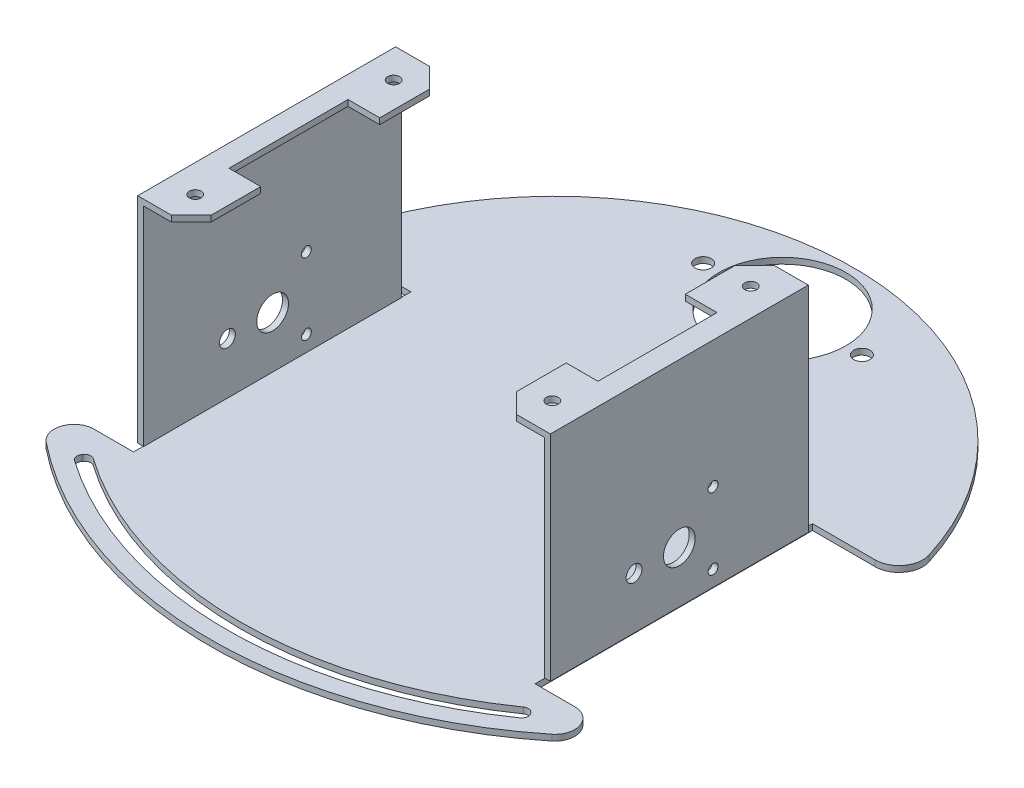
SolidWorks part; units mm, degrees
material "3.3535 (EN-AW 5754)"
ref_plane "Спереди" through (0, 0, 0) normal (0, 0, 1) x (1, 0, 0)
ref_plane "Сверху" through (0, 0, 0) normal (0, 1, 0) x (1, 0, 0)
ref_plane "Справа" through (0, 0, 0) normal (1, 0, 0) x (0, 0, -1)
sketch "Эскиз1" plane through (0, 0, 0) normal (0, 1, 0) x (1, 0, 0)
  line L0 (-50.6, 0) -> (-50.6, 34.95)
  line L1 (-50.6, 0) -> (-50.6, -34.95)
  line L2 (-50.6, -34.95) -> (-56.7978, -34.95)
  line L3 (50.6, 0) -> (50.6, 34.95)
  line L4 (50.6, 0) -> (50.6, -34.95)
  line L5 (50.6, -34.95) -> (60.5883, -34.95)
  line L14 (50.6, 34.95) -> (66.053, 34.95)
  line L15 (50.6, 34.95) -> (66.3145, 34.95)
  line L16 (50.6, 34.95) -> (66.053, 34.95)
  line L17 (50.6, 34.95) -> (66.4232, 34.95)
  line L18 (-50.6, 34.95) -> (-66.4232, 34.95)
  line L19 (-50.6, -34.95) -> (-60.5883, -34.95)
  line L20 (0, 0) -> (0, 1) construction
  line L21 (0, 0) -> (1, 0) construction
  arc A0 (72.1576, 42.7155) -> (-72.1576, 42.7155) centre (0, 20.5) ccw
  circle A1 centre (0, 78) radius 16
  arc A2 (-72.1576, 42.7155) -> (-66.4232, 34.95) centre (-66.4232, 40.95) ccw
  arc A3 (66.4232, 34.95) -> (72.1576, 42.7155) centre (66.4232, 40.95) ccw
  arc A4 (-60.5883, -34.95) -> (-63.7114, -43.8546) centre (-60.5883, -39.95) ccw
  arc A5 (63.7114, -43.8546) -> (60.5883, -34.95) centre (60.5883, -39.95) ccw
  arc A6 (-63.7114, -43.8546) -> (63.7114, -43.8546) centre (0, 35.8) ccw
extrude "Бобышка-Вытянуть1" add sketch "Эскиз1" along normal blind 1.5
sketch "Эскиз3" plane through (0, 0, 0) normal (0, 1, 0) x (1, 0, 0)
  line L0 (-52, 0) -> (-52, 32.5)
  line L1 (-52, 32.5) -> (-50.5, 32.5)
  line L2 (-50.5, 32.5) -> (-50.5, -32.5)
  line L3 (-50.5, -32.5) -> (-52, -32.5)
  line L4 (-52, -32.5) -> (-52, 0)
  line L5 (0, 0) -> (0, -12.5711) construction
  line L6 (0, 0) -> (8.0553, 0) construction
  line L7 (52, -32.5) -> (52, 0)
  line L8 (50.5, -32.5) -> (52, -32.5)
  line L9 (50.5, 32.5) -> (50.5, -32.5)
  line L10 (52, 32.5) -> (50.5, 32.5)
  line L11 (52, 0) -> (52, 32.5)
  dimension "D1" = 1.5
  dimension "D2" = 32.5
  dimension "D3" = 65
  dimension "D4" = 1.5
extrude "Бобышка-Вытянуть2" add sketch "Эскиз3" along normal blind 53.5 from offset 1.5
sketch "Эскиз5" plane through (0, 0, 0) normal (1, 0, 0) x (0, 0, -1)
  line L0 (0, 0) -> (0, 14.5) construction
  circle A0 centre (0, 14.5) radius 4
  dimension "D1" = 14.5
extrude "Вырез-Вытянуть1" cut sketch "Эскиз5" against normal through all and the other way blind 54
sketch "Эскиз6" plane through (0, 0, 0) normal (0, 1, 0) x (1, 0, 0)
  line L0 (0, 0) -> (0, 32.0086) construction
  line L1 (-3.4237, 0) -> (71.1887, 0) construction
  line L3 (-52, 32.5) -> (-52, -32.5) construction
  line L4 (-52, 0) -> (-52, 32.5)
  line L5 (-52, 32.5) -> (-38.5, 32.5)
  line L6 (-38.5, 32.5) -> (-38.5, 0)
  line L7 (-52, 0) -> (-52, -32.5)
  line L8 (-52, -32.5) -> (-38.5, -32.5)
  line L9 (-38.5, -32.5) -> (-38.5, 0)
  line L10 (-38.5, 15) -> (-46.5, 15)
  line L11 (-46.5, 15) -> (-46.5, 0)
  line L12 (-38.5, -15) -> (-46.5, -15)
  line L13 (-46.5, -15) -> (-46.5, 0)
  line L14 (46.5, -15) -> (46.5, 0)
  line L15 (38.5, -15) -> (46.5, -15)
  line L16 (46.5, 15) -> (46.5, 0)
  line L17 (38.5, 15) -> (46.5, 15)
  line L18 (38.5, -32.5) -> (38.5, 0)
  line L19 (52, -32.5) -> (38.5, -32.5)
  line L20 (52, 0) -> (52, -32.5)
  line L21 (38.5, 32.5) -> (38.5, 0)
  line L22 (52, 32.5) -> (38.5, 32.5)
  line L23 (52, 0) -> (52, 32.5)
  dimension "D2" = 30
  dimension "D1" = 13.5
  dimension "D3" = 15
  dimension "D4" = 8
  dimension "D5" = 8
extrude "Бобышка-Вытянуть3" add sketch "Эскиз6" against normal blind 1.5 from offset 55.5 contours L12 L13 L11 L10 L6 L5 L4 L7 L8 L9 | L20 L23 L22 L21 L17 L16 L14 L15 L18 L19
sketch "Эскиз9" plane through (0, 0, 0) normal (0, 1, 0) x (1, 0, 0)
  line L0 (45, 0) -> (-45, 0) construction
  line L1 (-45, -25) -> (-45, 25) construction
  line L2 (0, 0) -> (0, 4.277) construction
  line L3 (45, -25) -> (45, 25) construction
  circle A0 centre (-45, 25) radius 1.5
  circle A1 centre (-45, -25) radius 1.5
  circle A2 centre (45, -25) radius 1.5
  circle A3 centre (45, 25) radius 1.5
  point P12 (0, 0)
  dimension "D1" = 25
  dimension "D2" = 45
extrude "Вырез-Вытянуть2" cut sketch "Эскиз9" along normal through all from offset 50
sketch "Эскиз11" plane through (0, 1.5, 0) normal (0, 1, 0) x (1, 0, 0)
  circle A0 centre (0, 78) radius 20 construction
  circle A1 centre (20, 78) radius 2.05
  circle A2 centre (-20, 78) radius 2.05
  dimension "D1" = 40
  dimension "D2" = 4.1
  dimension "D3" = 4.1
extrude "Вырез-Вытянуть3" cut sketch "Эскиз11" against normal through all
chamfer "Фаска1" distance 5 angle 45 4 edges at (38.5, 54.75, 32.5) (38.5, 54.75, -32.5) (-38.5, 54.75, -32.5) (-38.5, 54.75, 32.5)
sketch "Эскиз12" plane through (0, 0, 0) normal (1, 0, 0) x (0, 0, -1)
  line L2 (0, 14.5) -> (-11.4, 14.5) construction
  line L5 (0, 14.5) -> (8.5, 14.5) construction
  line L6 (8.5, 14.5) -> (8.5, 23.5) construction
  line L7 (8.5, 14.5) -> (8.5, 5.5) construction
  circle A4 centre (-11.4, 14.5) radius 2
  circle A7 centre (8.5, 23.5) radius 1.25
  circle A8 centre (8.5, 5.5) radius 1.25
  dimension "D1" = 2.5
  dimension "D2" = 2.5
  dimension "D3" = 4
  dimension "D4" = 11.4
  dimension "D5" = 8.5
  dimension "D6" = 9
  dimension "D7" = 9
extrude "Вырез-Вытянуть4" cut sketch "Эскиз12" against normal through all both and the other way through all
sketch "Эскиз13" plane through (0, 1.5, 0) normal (0, 1, 0) x (1, 0, 0)
  line L0 (0, 0) -> (0, -12.4995) construction
  line L1 (0, -58.6) -> (0, -62)
  line L2 (0, 35.8) -> (179.8623, -211.7592)
  line L3 (0, 35.8) -> (-179.8623, -211.7592)
  circle A2 centre (0, 35.8) radius 97.8
  circle A3 centre (0, 35.8) radius 94.4
  arc A4 (-63.7114, -43.8546) -> (63.7114, -43.8546) centre (0, 35.8) ccw construction
  circle A6 centre (0, 35.8) radius 96.1 construction
  point P2 (0, -58.6)
  point P4 (0, -62)
  point P7 (0, -66.2)
  point P10 (0, -60.3)
  dimension "D1" = 35.8
  dimension "D2" = 195.6
  dimension "D3" = 188.8
  dimension "D4" = 3.4
  dimension "D5" = 4.2
extrude "Вырез-Вытянуть5" cut sketch "Эскиз13" against normal blind 10 contours A3 L3 A2 L1 | A3 L1 A2 L2
fillet "Скругление1" radius 1.6 4 edges at (-55.4869, 0.75, 40.5712) (-57.4854, 0.75, 43.3219) (57.4854, 0.75, 43.3219) (55.4869, 0.75, 40.5712)
